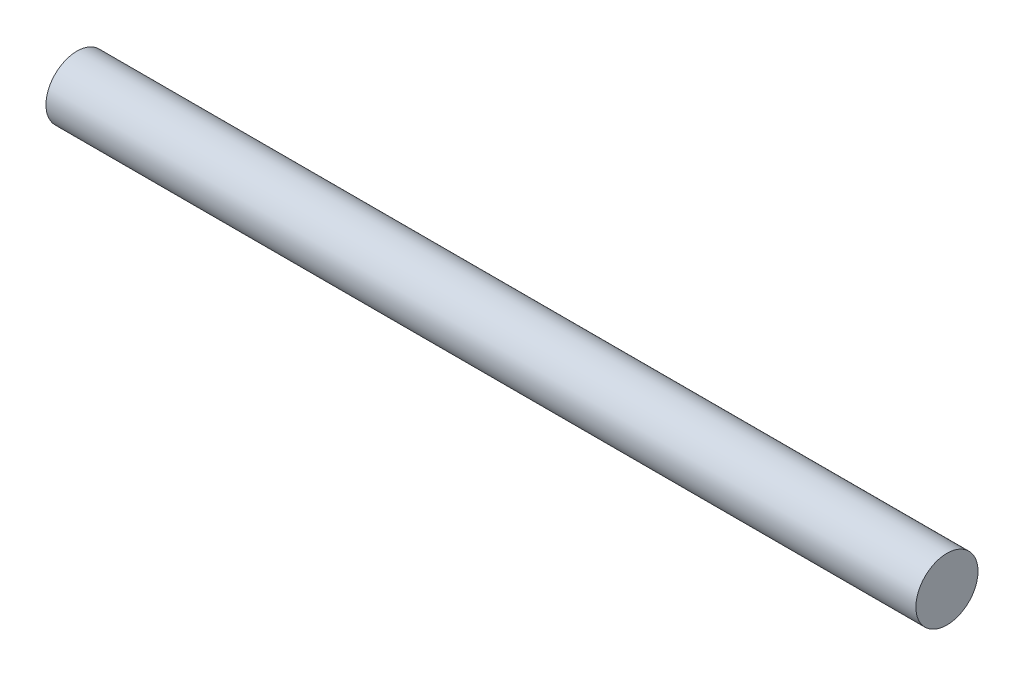
SolidWorks part; units mm, degrees
ref_plane "Front Plane" through (0, 0, 0) normal (0, 0, 1) x (1, 0, 0)
ref_plane "Top Plane" through (0, 0, 0) normal (0, 1, 0) x (1, 0, 0)
ref_plane "Right Plane" through (0, 0, 0) normal (1, 0, 0) x (0, 0, -1)
sketch "Sketch1" plane through (0, 0, 0) normal (1, 0, 0) x (0, 0, -1)
  circle A0 centre (0, 0) radius 0.5
  dimension "D1" = 1
extrude "Boss-Extrude1" add sketch "Sketch1" along normal blind 14
